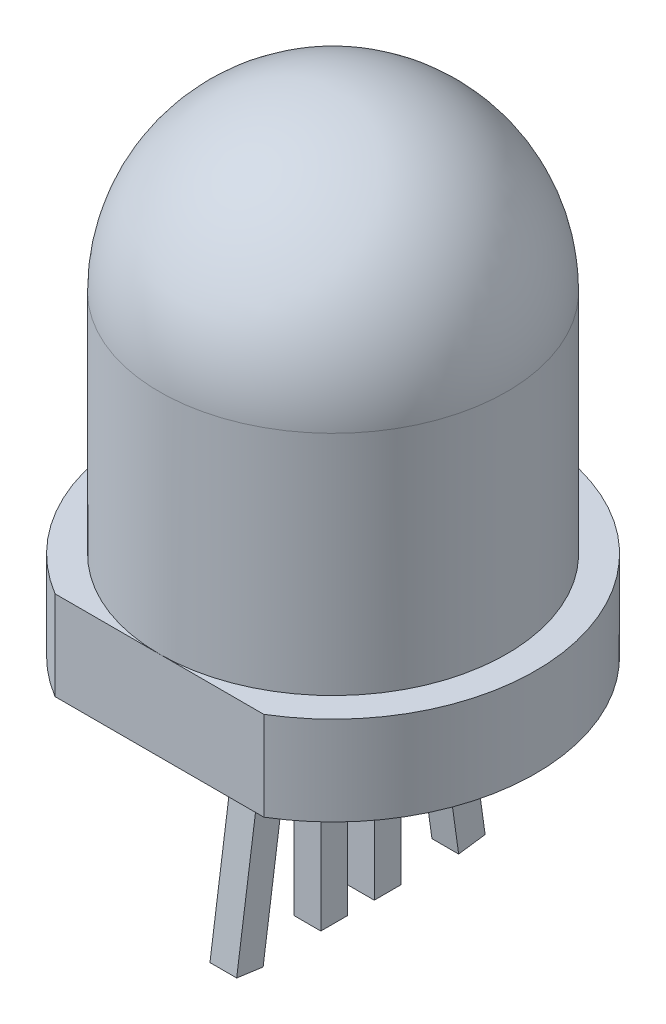
SolidWorks part; units mm, degrees
ref_plane "Plan de face" through (0, 0, 0) normal (0, 0, 1) x (1, 0, 0)
ref_plane "Plan de dessus" through (0, 0, 0) normal (0, 1, 0) x (1, 0, 0)
ref_plane "Plan de droite" through (0, 0, 0) normal (1, 0, 0) x (0, 0, -1)
sketch "Esquisse1" plane through (0, 0, 0) normal (0, 1, 0) x (1, 0, 0)
  circle A0 centre (0, 0) radius 3.9
  dimension "D1" = 7.8
extrude "Boss.-Extru.1" add sketch "Esquisse1" along normal blind 9
fillet "Congé1" radius 3.9 1 edges at (0, 9, 3.9)
sketch "Esquisse2" plane through (0, 0, 0) normal (0, -1, 0) x (1, 0, 0)
  line L1 (2.3436, 3.9) -> (-2.3436, 3.9)
  arc A0 (-2.3436, 3.9) -> (2.3436, 3.9) centre (0, 0) ccw
  circle A2 centre (0, 0) radius 3.9 construction
  dimension "D1" = 9.1
extrude "Boss.-Extru.2" add sketch "Esquisse2" along normal blind 2
sketch "Esquisse3" plane through (0, -2, 0) normal (0, -1, 0) x (1, 0, 0)
  line L0 (0, 3.9) -> (0, -4.55) construction
  line L1 (2.3436, 3.9) -> (-2.3436, 3.9) construction
  line L2 (0, -0.625) -> (0, -1.225) construction
  line L3 (-0.3, -0.025) -> (0.3, -0.025)
  line L4 (-0.3, -0.025) -> (-0.3, 0.575)
  line L5 (-0.3, 0.575) -> (0.3, 0.575)
  line L6 (0.3, -0.025) -> (0.3, 0.575)
  line L7 (0.3, -1.225) -> (-0.3, -1.225)
  line L8 (0.3, -1.225) -> (0.3, -0.625)
  line L9 (0.3, -0.625) -> (-0.3, -0.625)
  line L10 (-0.3, -1.225) -> (-0.3, -0.625)
  line L11 (0, -0.025) -> (0, 0.575) construction
  line L12 (0, -0.025) -> (0, -0.625) construction
  line L13 (-0.3, -0.025) -> (-0.3, -0.625) construction
  line L14 (-0.3, -0.325) -> (0, -0.325) construction
  arc A0 (-2.3436, 3.9) -> (2.3436, 3.9) centre (0, 0) ccw construction
  point P17 (0, -0.925)
  point P20 (0, 0.275)
  point P21 (0, 0.275)
  point P22 (0, -0.925)
  point P25 (0, -0.325)
  dimension "D1" = 1.2
  dimension "D2" = 0.6
  dimension "D3" = 0.6
  dimension "D4" = 0.6
  dimension "D5" = 0.6
extrude "Boss.-Extru.3" add sketch "Esquisse3" along normal blind 4.9
sketch "Esquisse5" plane through (0, -2, 0) normal (0, -1, 0) x (1, 0, 0)
  line L0 (0, 3.9) -> (0, 0.575) construction
  line L1 (2.3436, 3.9) -> (-2.3436, 3.9) construction
  line L2 (0.3, 0.575) -> (-0.3, 0.575) construction
  line L3 (-0.4685, 1.175) -> (0.4478, 1.175) construction
  dimension "D1" = 0.6
ref_plane "Plan1" through (0, -2.1232, 0.2984) normal (0, -0.9903, 0.1392) x (-1, 0, 0)
sketch "Esquisse6" plane through (0, -2.1232, 0.2984) normal (0, -0.9903, 0.1392) x (-1, 0, 0)
  line L0 (0.4685, -0.8852) -> (-0.4478, -0.8852) construction
  line L1 (-0.3, -0.8852) -> (0.3, -0.8852)
  line L2 (-0.3, -0.8852) -> (-0.3, -1.4852)
  line L3 (-0.3, -1.4852) -> (0.3, -1.4852)
  line L4 (0.3, -0.8852) -> (0.3, -1.4852)
  line L5 (0, -0.8852) -> (0, -1.4852) construction
  line L6 (0, -3.5837) -> (0, -0.2911) construction
  point P8 (0, -1.1852)
  point P9 (0, -1.1852)
  dimension "D1" = 0.6
  dimension "D2" = 0.6
extrude "Boss.-Extru.4" add sketch "Esquisse6" along normal blind 5
sketch "Esquisse7" plane through (0, -2, 0) normal (0, -1, 0) x (1, 0, 0)
  line L0 (0, -1.225) -> (0, -4.55) construction
  line L1 (-0.3, -1.225) -> (0.3, -1.225) construction
  line L2 (-0.3695, -1.825) -> (0.3997, -1.825) construction
  arc A0 (-2.3436, 3.9) -> (2.3436, 3.9) centre (0, 0) ccw construction
  dimension "D1" = 0.6
ref_plane "Plan2" through (0, -2.2128, -0.311) normal (0, -0.9903, -0.1392) x (-1, 0, 0)
sketch "Esquisse8" plane through (0, -2.2128, -0.311) normal (0, -0.9903, -0.1392) x (-1, 0, 0)
  line L0 (0, 2.1289) -> (0, 1.5289) construction
  line L1 (-0.3, 1.5289) -> (0.3, 1.5289)
  line L2 (-0.3, 1.5289) -> (-0.3, 2.1289)
  line L3 (-0.3, 2.1289) -> (0.3, 2.1289)
  line L4 (0.3, 1.5289) -> (0.3, 2.1289)
  line L5 (0, 0.9347) -> (0, 4.2274) construction
  point P7 (0, 1.8289)
  dimension "D1" = 0.6
  dimension "D2" = 0.6
extrude "Boss.-Extru.5" add sketch "Esquisse8" along normal blind 5
